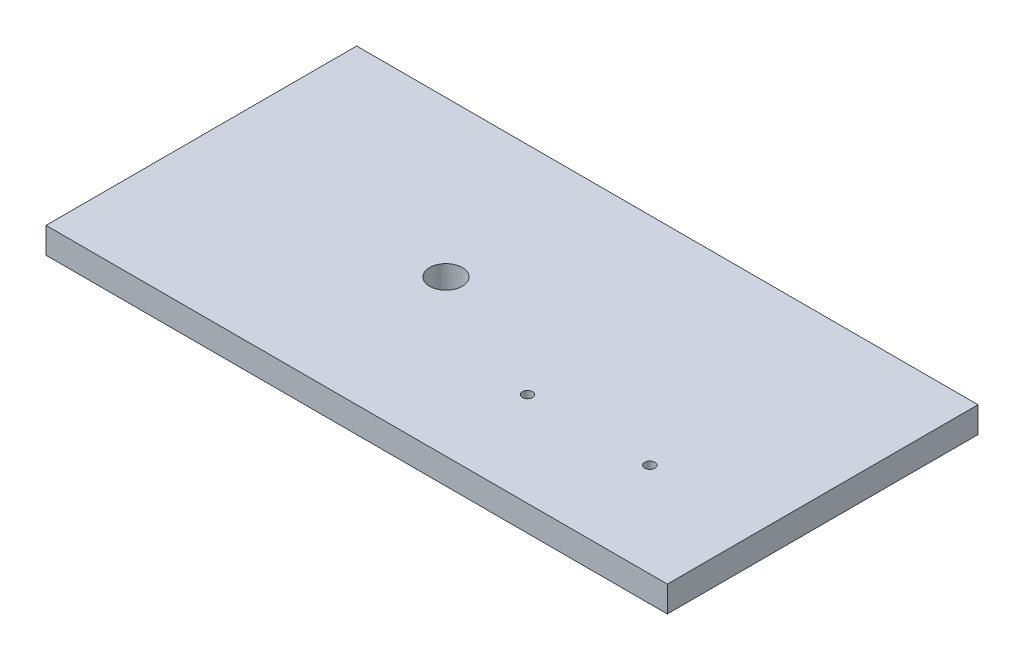
SolidWorks part; units mm, degrees
ref_plane "Front Plane" through (0, 0, 0) normal (0, 0, 1) x (1, 0, 0)
ref_plane "Top Plane" through (0, 0, 0) normal (0, 1, 0) x (1, 0, 0)
ref_plane "Right Plane" through (0, 0, 0) normal (1, 0, 0) x (0, 0, -1)
sketch "Sketch1" plane through (0, 0, 0) normal (0, 1, 0) x (1, 0, 0)
  line L1 (0, 0) -> (304.8, 0)
  line L2 (0, 0) -> (0, -152.4)
  line L3 (0, -152.4) -> (304.8, -152.4)
  line L4 (304.8, 0) -> (304.8, -152.4)
  dimension "D1" = 304.8
  dimension "D2" = 152.4
extrude "Boss-Extrude1" add sketch "Sketch1" along normal blind 12.7
sketch "Sketch2" plane through (0, 12.7, 0) normal (0, 1, 0) x (1, 0, 0)
  line L0 (0, 0) -> (0, -152.4) construction
  line L1 (190, -106.2) -> (250, -106.2) construction
  circle A0 centre (120, -76.2) radius 8
  circle A1 centre (250, -106.2) radius 2.5
  circle A2 centre (190, -106.2) radius 2.5
  point P6 (0, -76.2)
  point P11 (220, -106.2)
  dimension "D2" = 16
  dimension "D3" = 5
  dimension "D1" = 120
  dimension "D4" = 100
  dimension "D5" = 60
  dimension "D6" = 30
extrude "Cut-Extrude1" cut sketch "Sketch2" against normal through all
